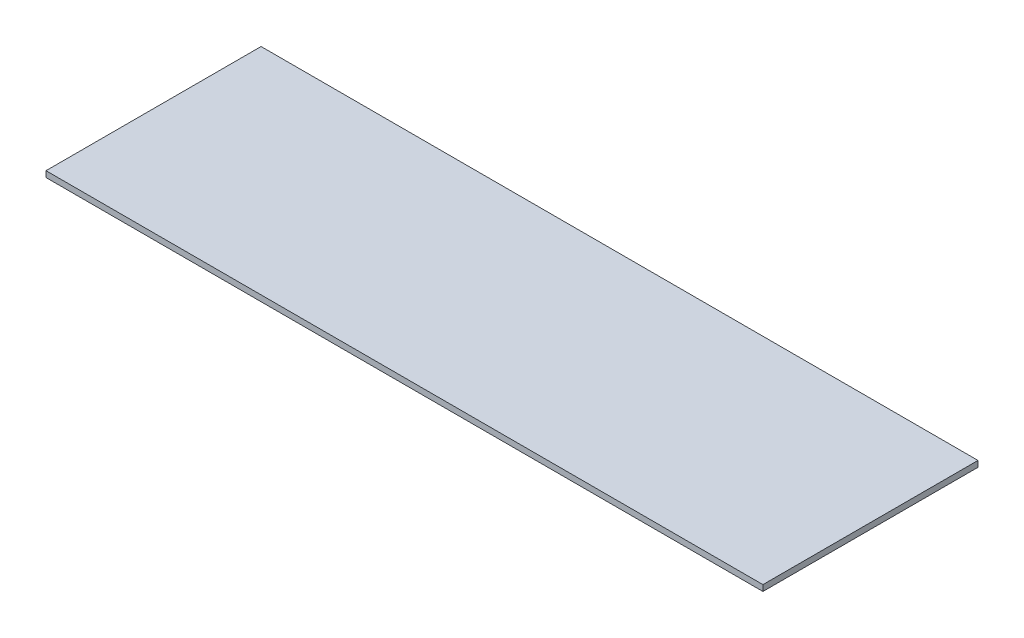
SolidWorks part; units mm, degrees
ref_plane "Спереди" through (0, 0, 0) normal (0, 0, 1) x (1, 0, 0)
ref_plane "Сверху" through (0, 0, 0) normal (0, 1, 0) x (1, 0, 0)
ref_plane "Справа" through (0, 0, 0) normal (1, 0, 0) x (0, 0, -1)
sketch "Эскиз1" plane through (0, 0, 0) normal (0, 1, 0) x (1, 0, 0)
  line L1 (-600, 180) -> (600, 180)
  line L2 (-600, 180) -> (-600, -180)
  line L3 (-600, -180) -> (600, -180)
  line L4 (600, 180) -> (600, -180)
  line L5 (-600, 180) -> (600, -180) construction
  line L6 (-600, -180) -> (600, 180) construction
  point P0 (0, 0)
extrude "Бобышка-Вытянуть1" add sketch "Эскиз1" along normal blind 10
